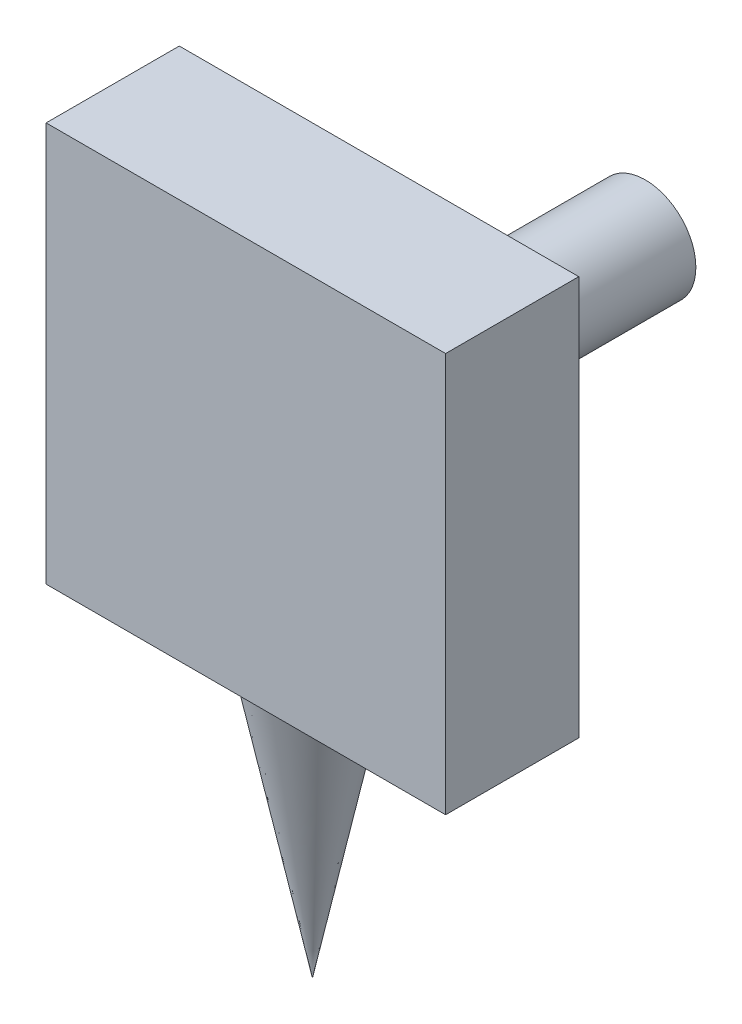
SolidWorks part; units mm, degrees
ref_plane "Front Plane" through (0, 0, 0) normal (0, 0, 1) x (1, 0, 0)
ref_plane "Top Plane" through (0, 0, 0) normal (0, 1, 0) x (1, 0, 0)
ref_plane "Right Plane" through (0, 0, 0) normal (1, 0, 0) x (0, 0, -1)
sketch "Sketch1" plane through (0, 0, 0) normal (0, 0, 1) x (1, 0, 0)
  circle A0 centre (126.973, 125.7306) radius 3.795
  dimension "D1" = 7.59
extrude "Boss-Extrude1" add sketch "Sketch1" against normal blind 20
ref_plane "Plane1" through (0, 0, -10) normal (0, 0, 1) x (1, 0, 0)
sketch "Sketch2" plane through (0, 0, 0) normal (0, 0, 1) x (1, 0, 0)
  line L1 (111.973, 110.7306) -> (141.973, 110.7306)
  line L2 (111.973, 110.7306) -> (111.973, 140.7306)
  line L3 (111.973, 140.7306) -> (141.973, 140.7306)
  line L4 (141.973, 110.7306) -> (141.973, 140.7306)
  line L5 (111.973, 110.7306) -> (141.973, 140.7306) construction
  line L6 (111.973, 140.7306) -> (141.973, 110.7306) construction
  circle A0 centre (126.973, 125.7306) radius 3.795 construction
  point P0 (126.973, 125.7306)
  dimension "D1" = 30
  dimension "D2" = 30
extrude "Boss-Extrude2" add sketch "Sketch2" along normal blind 10
ref_plane "Plane2" through (126.973, 0, 0) normal (1, 0, 0) x (0, 0, -1)
sketch "Sketch3" plane through (126.973, 0, 0) normal (1, 0, 0) x (0, 0, -1)
  line L0 (-0.7585, 110.7306) -> (-5, 90.1171)
  line L1 (-10, 110.7306) -> (0, 110.7306) construction
  line L2 (-5, 90.1171) -> (-5, 110.7306)
  line L3 (-5, 110.7306) -> (-0.7585, 110.7306)
revolve "Revolve1" add sketch "Sketch3" angle 360 about L2
